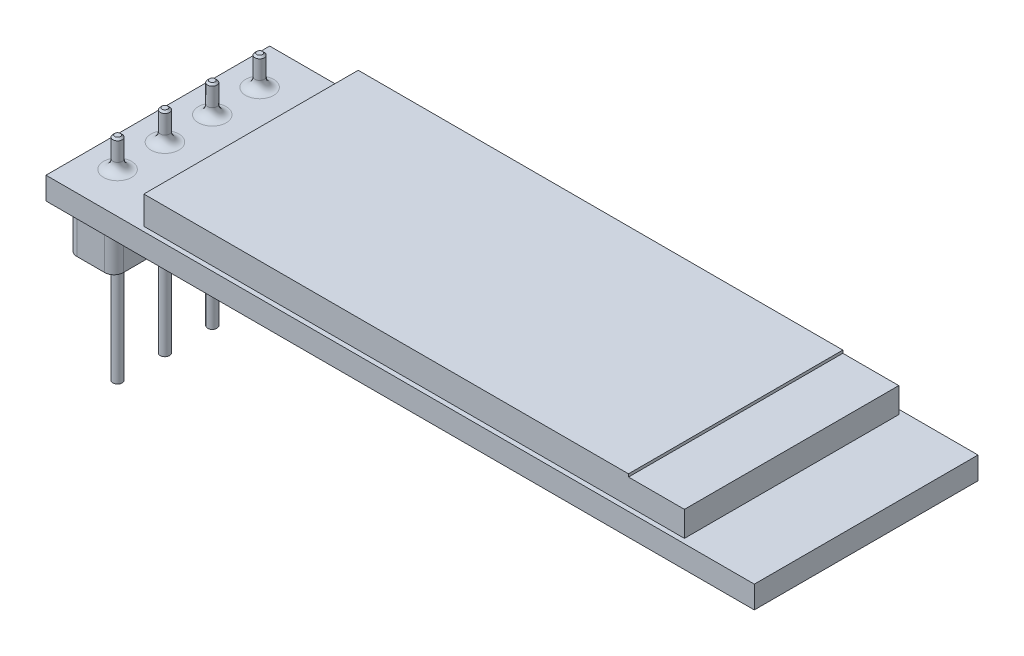
SolidWorks part; units mm, degrees
ref_plane "Front Plane" through (0, 0, 0) normal (0, 0, 1) x (1, 0, 0)
ref_plane "Top Plane" through (0, 0, 0) normal (0, 1, 0) x (1, 0, 0)
ref_plane "Right Plane" through (0, 0, 0) normal (1, 0, 0) x (0, 0, -1)
sketch "Sketch1" plane through (0, 0, 0) normal (0, 1, 0) x (1, 0, 0)
  line L1 (-19, -6) -> (19, -6)
  line L2 (-19, -6) -> (-19, 6)
  line L3 (-19, 6) -> (19, 6)
  line L4 (19, -6) -> (19, 6)
  line L5 (-19, -6) -> (19, 6) construction
  line L6 (-19, 6) -> (19, -6) construction
  point P0 (0, 0)
  dimension "D1" = 38
  dimension "D2" = 12
extrude "Boss-Extrude1" add sketch "Sketch1" along normal blind 1.2
sketch "Sketch2" plane through (0, 1.2, 0) normal (0, 1, 0) x (1, 0, 0)
  line L0 (-19, 0) -> (19, 0) construction
  line L1 (-19, 6) -> (-19, -6) construction
  line L2 (19, -6) -> (19, 6) construction
  line L4 (-14, -5.75) -> (15, -5.75)
  line L5 (-14, -5.75) -> (-14, 5.75)
  line L6 (-14, 5.75) -> (15, 5.75)
  line L7 (15, -5.75) -> (15, 5.75)
  line L8 (-14, -5.75) -> (15, 5.75) construction
  line L9 (-14, 5.75) -> (15, -5.75) construction
  point P6 (0.5, 0)
  dimension "D1" = 29
  dimension "D2" = 11.5
  dimension "D3" = 5
extrude "Boss-Extrude2" add sketch "Sketch2" along normal blind 1.5
sketch "Sketch3" plane through (0, 1.2, 0) normal (0, 1, 0) x (1, 0, 0)
  line L0 (-19, 0) -> (19, 0) construction
  line L1 (-19, 6) -> (-19, -6) construction
  line L2 (19, -6) -> (19, 6) construction
  line L3 (-19, -3.81) -> (19, -3.81) construction
  line L4 (-17.6, -6) -> (-17.6, 6) construction
  line L5 (-19, -6) -> (19, -6) construction
  line L6 (19, 6) -> (-19, 6) construction
  circle A0 centre (-17.35, -3.81) radius 0.25
  dimension "D2" = 0.5
  dimension "D1" = 3.81
  dimension "D3" = 1.4
extrude "Boss-Extrude3" add sketch "Sketch3" along normal blind 1.6 and the other way blind 9.8
chamfer "Chamfer1" distance 0.1 angle 45 1 edges at (-17.35, 2.8, 4.06)
fillet "Fillet1" radius 0.5 1 edges at (-17.35, 1.2, 3.56)
pattern_linear "LPattern1" count 4 spacing 2.54 along (0, 0, -1) of "Boss-Extrude3", "Chamfer1", "Fillet1"
sketch "Sketch4" plane through (0, 0, 0) normal (0, -1, 0) x (1, 0, 0)
  line L0 (-17.35, 4.06) -> (-17.35, -4.06) construction
  line L3 (-19, 0) -> (0, 0) construction
  line L4 (-18.6, 5.25) -> (-16.1, 5.25)
  line L5 (-18.6, 5.25) -> (-18.6, -5.25)
  line L6 (-18.6, -5.25) -> (-16.1, -5.25)
  line L7 (-16.1, 5.25) -> (-16.1, -5.25)
  line L8 (-18.6, 5.25) -> (-16.1, -5.25) construction
  line L9 (-18.6, -5.25) -> (-16.1, 5.25) construction
  line L10 (-19, -6) -> (-19, 6) construction
  circle A0 centre (-17.35, 3.81) radius 0.25 construction
  circle A1 centre (-17.35, 3.81) radius 0.25 construction
  circle A2 centre (-17.35, -3.81) radius 0.25 construction
  point P6 (-17.35, 0)
  point P19 (-17.35, 0)
  dimension "D1" = 2.5
  dimension "D2" = 10.5
extrude "Boss-Extrude4" add sketch "Sketch4" along normal blind 2.5
fillet "Fillet2" radius 0.5 4 edges at (-16.1, -1.25, 5.25) (-18.6, -1.25, 5.25) (-16.1, -1.25, -5.25) (-18.6, -1.25, -5.25)
sketch "Sketch5" plane through (0, 2.7, 0) normal (0, 1, 0) x (1, 0, 0)
  line L0 (-14, -5.75) -> (15, -5.75) construction
  line L1 (15, 5.75) -> (12, 5.75)
  line L2 (15, 5.75) -> (15, -5.75)
  line L3 (15, -5.75) -> (12, -5.75)
  line L4 (12, 5.75) -> (12, -5.75)
  dimension "D1" = 3
extrude "Cut-Extrude1" cut sketch "Sketch5" against normal blind 0.15
